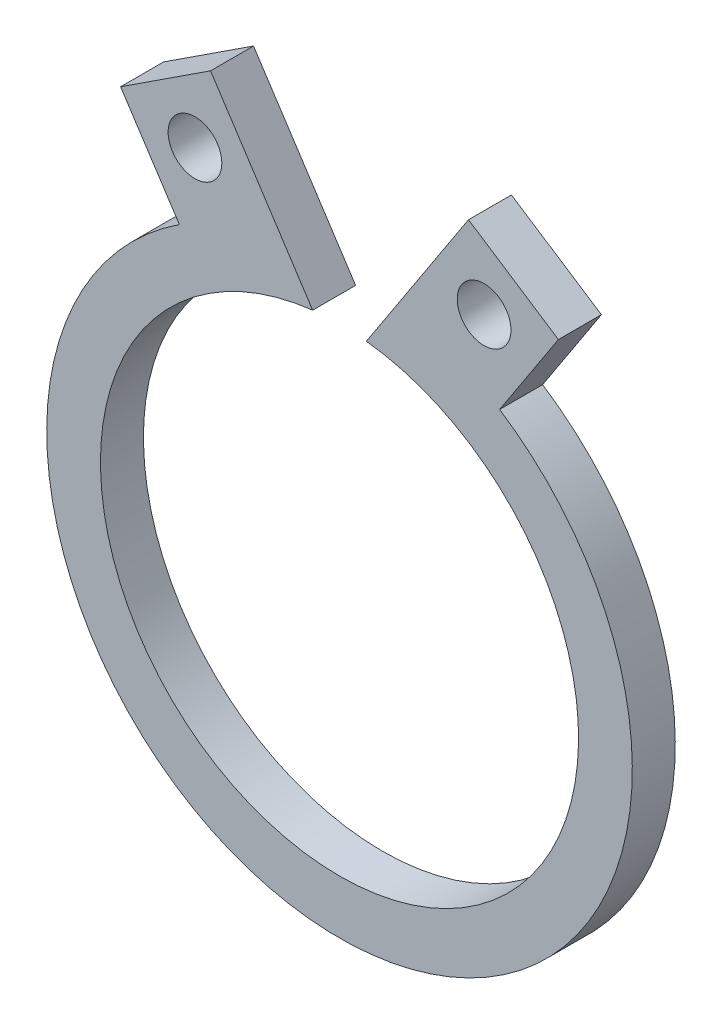
SolidWorks part; units mm, degrees
ref_plane "Front Plane" through (0, 0, 0) normal (0, 0, 1) x (1, 0, 0)
ref_plane "Top Plane" through (0, 0, 0) normal (0, 1, 0) x (1, 0, 0)
ref_plane "Right Plane" through (0, 0, 0) normal (1, 0, 0) x (0, 0, -1)
sketch "Sketch2" plane through (0, 0, 0) normal (0, 0, 1) x (1, 0, 0)
  line L0 (-4.0749, 6.2368) -> (-2.981, 4.5625)
  line L1 (-4.0749, 6.2368) -> (-2.4006, 7.3307)
  line L2 (-2.4006, 7.3307) -> (-0.5, 4.4218)
  line L3 (-0.5, 0) -> (-0.5, 2.7115) construction
  line L4 (0.5, 0) -> (0.5, 2.7115) construction
  line L5 (0, 0) -> (0, 50000) construction
  line L6 (4.0749, 6.2368) -> (2.981, 4.5625)
  line L7 (4.0749, 6.2368) -> (2.4006, 7.3307)
  line L8 (2.4006, 7.3307) -> (0.5, 4.4218)
  arc A0 (-0.5, 4.4218) -> (0.5, 4.4218) centre (0, 0) ccw
  arc A1 (-2.981, 4.5625) -> (2.981, 4.5625) centre (0, 0) ccw
  dimension "D1" = 10.9
  dimension "D2" = 8.9
  dimension "D3" = 2
  dimension "D4" = 2
  dimension "D5" = 0.5
  dimension "D6" = 0.5
  dimension "D7" = 2.7115
extrude "Boss-Extrude1" add sketch "Sketch2" along normal blind 0.8
sketch "Sketch3" plane through (0, 0, 0.8) normal (0, 0, 1) x (1, 0, 0)
  line L1 (-4.0749, 6.2368) -> (-2.981, 4.5625) construction
  line L2 (-2.4006, 7.3307) -> (-4.0749, 6.2368) construction
  line L3 (2.981, 4.5625) -> (4.0749, 6.2368) construction
  line L5 (4.0749, 6.2368) -> (2.4006, 7.3307) construction
  circle A0 centre (-2.6908, 5.9466) radius 0.5
  circle A1 centre (2.6908, 5.9466) radius 0.5
  point P11 (0, 0)
  point P13 (3.2247, 6.7923)
  dimension "D1" = 1
  dimension "D2" = 1
  dimension "D3" = 1
  dimension "D4" = 1
  dimension "D5" = 1
  dimension "D6" = 1
extrude "Cut-Extrude1" cut sketch "Sketch3" against normal through all contours A0 | A1
equation "\"Inner Diameter\"= 8.9mm"
equation "\"Outer Diameter\"= \"Inner Diameter\" + 2mm"
equation "\"D1@Sketch2\"=\"Outer Diameter\""
equation "\"D2@Sketch2\"=\"Inner Diameter\""
equation "\"D6@Sketch2\"=\"D5@Sketch2\""
equation "\"D2@Sketch3\"=\"D1@Sketch3\""
